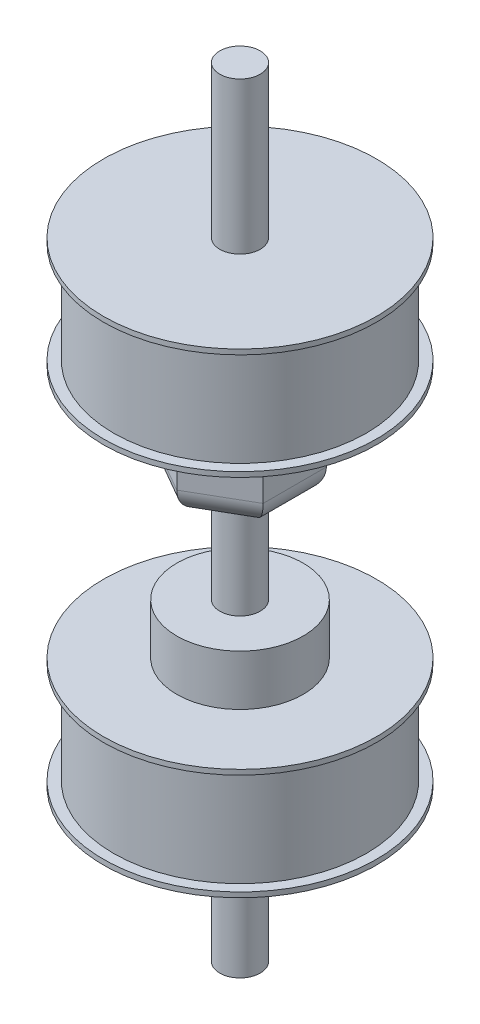
SolidWorks part; units mm, degrees
ref_plane "Front Plane" through (0, 0, 0) normal (0, 0, 1) x (1, 0, 0)
ref_plane "Top Plane" through (0, 0, 0) normal (0, 1, 0) x (1, 0, 0)
ref_plane "Right Plane" through (0, 0, 0) normal (1, 0, 0) x (0, 0, -1)
sketch "Sketch2" plane through (0, 0, 0) normal (0, 1, 0) x (1, 0, 0)
  circle A0 centre (0, 0) radius 27
  point P3 (0, 0)
extrude "Boss-Extrude1" add sketch "Sketch2" along normal blind 1
ref_plane "Plane1" through (0, 1, 0) normal (0, 1, 0) x (1, 0, 0)
sketch "Sketch3" plane through (0, 1, 0) normal (0, 1, 0) x (1, 0, 0)
  circle A0 centre (0, 0) radius 12.5
extrude "Boss-Extrude2" add sketch "Sketch3" along normal blind 10
ref_plane "Plane2" through (0, 11, 0) normal (0, 1, 0) x (1, 0, 0)
sketch "Sketch4" plane through (0, 11, 0) normal (0, 1, 0) x (1, 0, 0)
  circle A0 centre (0, 0) radius 4
extrude "Boss-Extrude3" add sketch "Sketch4" along normal blind 20
ref_plane "Plane3" through (0, 31, 0) normal (0, 1, 0) x (1, 0, 0)
sketch "Sketch5" plane through (0, 31, 0) normal (0, 1, 0) x (1, 0, 0)
  line L1 (0, 12.5) -> (10.8253, 6.25)
  line L3 (10.8253, 6.25) -> (10.8253, -6.25)
  line L4 (10.8253, -6.25) -> (0, -12.5)
  line L5 (0, -12.5) -> (-10.8253, -6.25)
  line L6 (-10.8253, -6.25) -> (-10.8253, 6.25)
  line L7 (-10.8253, 6.25) -> (0, 12.5)
  circle A0 centre (0, 0) radius 12.5 construction
  point P18 (0, 0)
extrude "Boss-Extrude4" add sketch "Sketch5" along normal blind 20
fillet "Fillet1" radius 5 6 edges at (-10.8253, 31, 0) (-5.4127, 31, 9.375) (5.4127, 31, 9.375) (10.8253, 31, 0) (5.4127, 31, -9.375) (-5.4127, 31, -9.375)
ref_plane "Plane4" through (0, 51, 0) normal (0, 1, 0) x (1, 0, 0)
sketch "Sketch6" plane through (0, 51, 0) normal (0, 1, 0) x (1, 0, 0)
  circle A0 centre (0, 0) radius 27
  dimension "D1" = 54
extrude "Boss-Extrude5" add sketch "Sketch6" along normal blind 1
ref_plane "Plane5" through (0, 52, 0) normal (0, 1, 0) x (1, 0, 0)
sketch "Sketch7" plane through (0, 52, 0) normal (0, 1, 0) x (1, 0, 0)
  circle A0 centre (0, 0) radius 25
extrude "Boss-Extrude6" add sketch "Sketch7" along normal blind 20
ref_plane "Plane6" through (0, 72, 0) normal (0, 1, 0) x (1, 0, 0)
sketch "Sketch8" plane through (0, 72, 0) normal (0, 1, 0) x (1, 0, 0)
  circle A0 centre (0, 0) radius 27
extrude "Boss-Extrude7" add sketch "Sketch8" along normal blind 1
ref_plane "Plane7" through (0, 73, 0) normal (0, 1, 0) x (1, 0, 0)
sketch "Sketch9" plane through (0, 73, 0) normal (0, 1, 0) x (1, 0, 0)
  circle A0 centre (0, 0) radius 4
extrude "Boss-Extrude8" add sketch "Sketch9" along normal blind 30
ref_plane "Plane8" through (0, 0, 0) normal (0, -1, 0) x (-1, 0, 0)
sketch "Sketch10" plane through (0, 0, 0) normal (0, -1, 0) x (-1, 0, 0)
  circle A0 centre (0, 0) radius 25
extrude "Boss-Extrude9" add sketch "Sketch10" along normal blind 20
ref_plane "Plane9" through (0, -20, 0) normal (0, -1, 0) x (-1, 0, 0)
sketch "Sketch11" plane through (0, -20, 0) normal (0, -1, 0) x (-1, 0, 0)
  circle A0 centre (0, 0) radius 27
extrude "Boss-Extrude10" add sketch "Sketch11" along normal blind 1
ref_plane "Plane10" through (0, -21, 0) normal (0, -1, 0) x (-1, 0, 0)
sketch "Sketch12" plane through (0, -21, 0) normal (0, -1, 0) x (-1, 0, 0)
  circle A0 centre (0, 0) radius 4
extrude "Boss-Extrude11" add sketch "Sketch12" along normal blind 30
